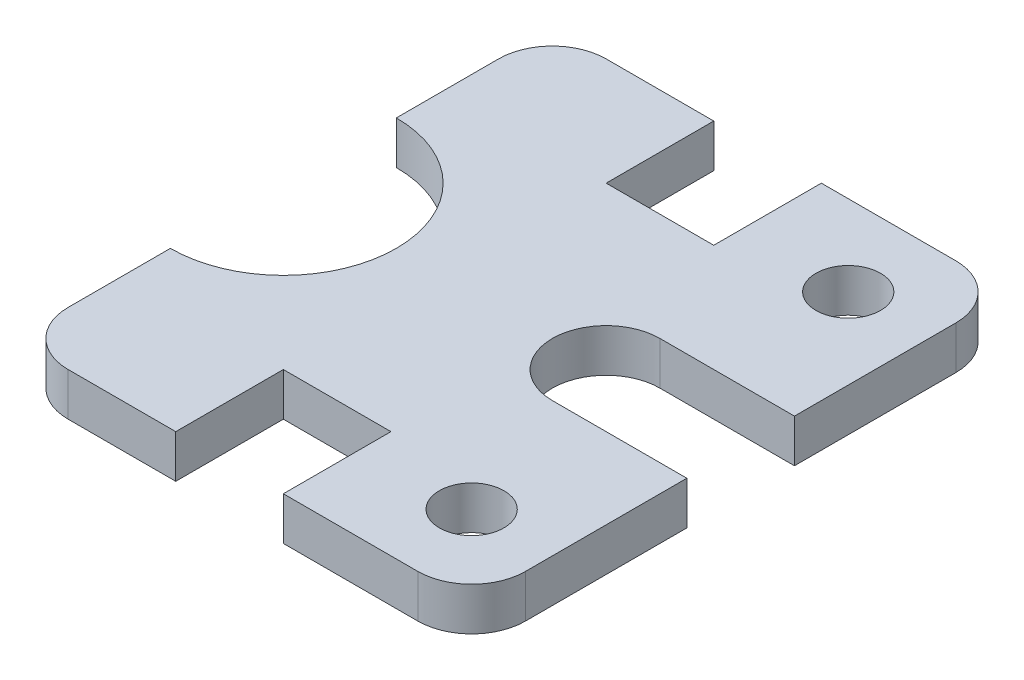
SolidWorks part; units mm, degrees
ref_plane "Front Plane" through (0, 0, 0) normal (0, 0, 1) x (1, 0, 0)
ref_plane "Top Plane" through (0, 0, 0) normal (0, 1, 0) x (1, 0, 0)
ref_plane "Right Plane" through (0, 0, 0) normal (1, 0, 0) x (0, 0, -1)
sketch "Sketch1" plane through (0, 0, 0) normal (0, 1, 0) x (1, 0, 0)
  line L0 (0, 0) -> (25, 0)
  line L1 (0, -20) -> (25, -20)
  line L2 (25, -20) -> (25, -50)
  line L3 (15, -60) -> (-10, -60)
  line L4 (-10, -60) -> (-10, -40)
  line L5 (-10, -40) -> (-30, -40)
  line L6 (-30, -40) -> (-30, -60)
  line L7 (-30, -60) -> (-50, -60)
  line L8 (-60, -50) -> (-60, -31)
  line L9 (-60, 11) -> (-60, 30)
  line L10 (-50, 40) -> (-30, 40)
  line L11 (-30, 40) -> (-30, 20)
  line L12 (-30, 20) -> (-10, 20)
  line L13 (-10, 20) -> (-10, 40)
  line L14 (-10, 40) -> (15, 40)
  line L15 (25, 30) -> (25, 0)
  line L16 (-10, -10) -> (-39, -10) construction
  arc A0 (0, 0) -> (0, -20) centre (0, -10) ccw
  arc A1 (-60, -31) -> (-60, 11) centre (-60, -10) ccw
  arc A2 (15, -60) -> (25, -50) centre (15, -50) ccw
  arc A3 (-60, 30) -> (-50, 40) centre (-50, 30) cw
  arc A4 (-50, -60) -> (-60, -50) centre (-50, -50) cw
  arc A5 (25, 30) -> (15, 40) centre (15, 30) ccw
  circle A6 centre (10, -45) radius 6
  circle A7 centre (10, 25) radius 6
  point P23 (25, -60)
  point P26 (-60, 40)
  point P29 (-60, -60)
  point P32 (25, 40)
  dimension "D1" = 10
  dimension "D4" = 35
  dimension "D9" = 21
  dimension "D18" = 10
  dimension "D19" = 10
  dimension "D20" = 10
  dimension "D21" = 10
  dimension "D22" = 12
  dimension "D25" = 12
  dimension "D2" = 25
  dimension "D3" = 25
  dimension "D5" = 20
  dimension "D6" = 20
  dimension "D7" = 20
  dimension "D8" = 85
  dimension "D10" = 50
  dimension "D11" = 50
  dimension "D12" = 100
  dimension "D13" = 85
  dimension "D14" = 35
  dimension "D15" = 20
  dimension "D16" = 20
  dimension "D17" = 20
  dimension "D23" = 15
  dimension "D24" = 15
  dimension "D26" = 15
  dimension "D27" = 15
extrude "Boss-Extrude1" add sketch "Sketch1" along normal blind 8
